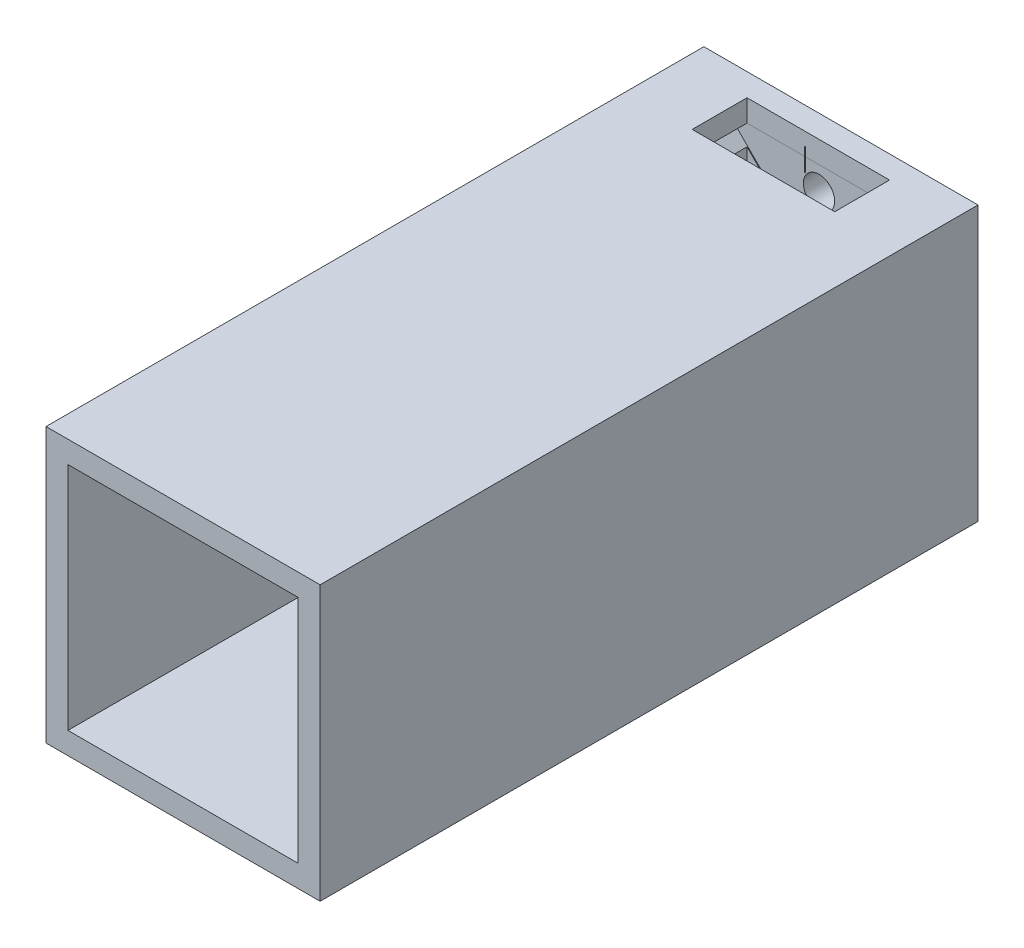
SolidWorks part; units mm, degrees
ref_plane "Front Plane" through (0, 0, 0) normal (0, 0, 1) x (1, 0, 0)
ref_plane "Top Plane" through (0, 0, 0) normal (0, 1, 0) x (1, 0, 0)
ref_plane "Right Plane" through (0, 0, 0) normal (1, 0, 0) x (0, 0, -1)
sketch "Sketch1" plane through (0, 0, 0) normal (0, 0, 1) x (1, 0, 0)
  line L1 (-12.5, -12.5) -> (12.5, -12.5)
  line L2 (-12.5, -12.5) -> (-12.5, 12.5)
  line L3 (-12.5, 12.5) -> (12.5, 12.5)
  line L4 (12.5, -12.5) -> (12.5, 12.5)
  line L5 (-12.5, -12.5) -> (12.5, 12.5) construction
  line L6 (-12.5, 12.5) -> (12.5, -12.5) construction
  point P0 (0, 0)
  dimension "D1" = 25
sketch "Sketch2" plane through (0, 0, 0) normal (0, 0, 1) x (1, 0, 0)
  line L5 (-12.5, -12.5) -> (12.5, 12.5) construction
  line L6 (-12.5, 12.5) -> (12.5, -12.5) construction
  circle A0 centre (0, 0) radius 2.5
  circle A1 centre (8.25, 0) radius 1.425
  circle A2 centre (0, -8.25) radius 1.425
  circle A3 centre (-8.25, 0) radius 1.425
  circle A4 centre (0, 8.25) radius 1.425
  point P0 (0, 0)
  dimension "D2" = 4
  dimension "D1" = 25
extrude "Boss-Extrude1" add sketch "Sketch1" along normal blind 60
shell "Shell1" thickness 2
extrude "Cut-Extrude4" cut sketch "Sketch2" along normal blind 2
sketch "Sketch4" plane through (0, 0, 2) normal (0, 0, 1) x (1, 0, 0)
  line L0 (0, 0) -> (-8.2, 0)
  line L1 (-5.7033, -6) -> (4.2967, -6)
  line L3 (-5.7033, 6) -> (4.2967, 6)
  line L5 (-5.7033, -6) -> (4.2967, 6) construction
  line L6 (-5.7033, 6) -> (4.2967, -6) construction
  line L7 (0, 0) -> (8.2, 0)
  line L8 (0, 0) -> (0, 6)
  line L9 (0, 0) -> (0, -6)
  line L11 (-10.5, 8.3787) -> (8.3787, -10.5)
  line L12 (-10.5, -10.5) -> (10.5, -10.5) construction
  line L13 (-8.3787, 10.5) -> (10.5, -8.3787)
  line L14 (10.5, -10.5) -> (10.5, 10.5) construction
  line L15 (-10.5, -8.3787) -> (8.3787, 10.5)
  line L16 (10.5, 10.5) -> (-10.5, 10.5) construction
  line L17 (-8.3787, -10.5) -> (10.5, 8.3787)
  line L19 (-9.5, -6.75) -> (9.5, -6.75)
  line L20 (-9.5, -6.75) -> (-9.5, 6.75)
  line L21 (-9.5, 6.75) -> (9.5, 6.75)
  line L22 (9.5, -6.75) -> (9.5, 6.75)
  line L23 (-9.5, -6.75) -> (9.5, 6.75) construction
  line L24 (-9.5, 6.75) -> (9.5, -6.75) construction
  arc A2 (-5.7033, -6) -> (-5.7033, 6) centre (0.2578, 0) cw
  arc A3 (4.2967, 6) -> (4.2967, -6) centre (1.6369, 0) cw
  point P0 (0, 0)
  point P12 (0, 0)
  point P22 (0, 0)
  point P25 (0, 0)
  point P28 (0, 0)
  point P33 (-1.0607, -1.0607)
  point P38 (1.0607, 1.0607)
  point P43 (-1.0607, 1.0607)
  point P46 (1.0607, -1.0607)
  circle M9 centre (8.25, 0) radius 1.425
  circle M11 centre (-8.25, 0) radius 1.425
  line M13 (10.5, -10.5) -> (10.5, 10.5)
  line M14 (10.5, 10.5) -> (-10.5, 10.5)
  line M15 (-10.5, 10.5) -> (-10.5, -10.5)
  line M16 (-10.5, -10.5) -> (10.5, -10.5)
  dimension "D1" = 19
extrude "Boss-Extrude3" add sketch "Sketch4" along normal blind 30 contours L11 A2 L3 L13 L21 | L11 L21 L13 M14 M15 | L21 L13 L3 L15 | L15 L21 L17 M13 M14 | L3 A3 L17 L21 L15 | L1 A2 L15 L19 L17 | L13 A3 L1 L11 L19 | L19 L15 L17 M15 M16 | L19 L11 L13 M16 M13 | L17 A3 L22 L21 M9 | A3 L13 L19 L22 M9 | L17 L19 L11 L1 | L15 A2 L20 L19 M11 | A2 L11 L21 L20 M11 | A2 L20 M11 | A3 L22 M9
sketch "Sketch5" plane through (0, 12.5, 0) normal (0, 1, 0) x (1, 0, 0)
  line L0 (0, 0) -> (0, -4.5668)
  line L2 (-6.5, -7.0668) -> (6.5, -7.0668)
  line L3 (-6.5, -7.0668) -> (-6.5, -2.0668)
  line L4 (-6.5, -2.0668) -> (6.5, -2.0668)
  line L5 (6.5, -7.0668) -> (6.5, -2.0668)
  line L6 (-6.5, -7.0668) -> (6.5, -2.0668) construction
  line L7 (-6.5, -2.0668) -> (6.5, -7.0668) construction
  circle A0 centre (0.0246, -3.3013) radius 0.0246
  point P3 (0.0246, -4.5668)
  dimension "D1" = 13
  dimension "D2" = 5
fillet "Fillet1" [suppressed] radius 2
extrude "Cut-Extrude6" cut sketch "Sketch5" against normal blind 10
